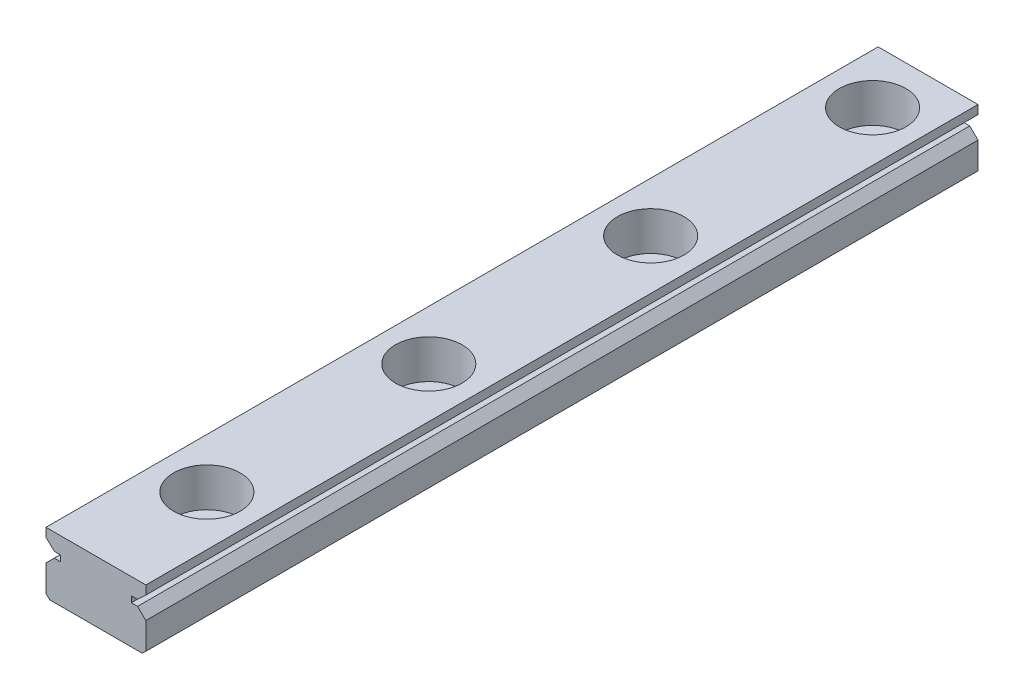
SolidWorks part; units mm, degrees
ref_plane "前视基准面" through (0, 0, 0) normal (0, 0, 1) x (1, 0, 0)
ref_plane "上视基准面" through (0, 0, 0) normal (0, 1, 0) x (1, 0, 0)
ref_plane "右视基准面" through (0, 0, 0) normal (1, 0, 0) x (0, 0, -1)
sketch "Model" plane through (0, 0, 0) normal (0, 0, 1) x (1, 0, 0)
  line L0 (172.467, 54.8604) -> (176.6229, 54.8604)
  line L1 (172.123, 60.3558) -> (176.6229, 60.3558)
  line L2 (172.123, 57.5787) -> (172.867, 58.3137)
  line L3 (172.867, 58.3137) -> (173.431, 58.3137)
  line L4 (173.431, 58.3137) -> (173.431, 58.8505)
  line L5 (173.431, 58.8505) -> (172.879, 58.8505)
  line L6 (172.879, 58.8505) -> (172.123, 59.563)
  line L7 (172.123, 55.1745) -> (172.123, 57.5787)
  line L8 (172.123, 59.563) -> (172.123, 60.3558)
  line L9 (172.123, 55.1745) -> (172.467, 54.8604)
  line L10 (180.7788, 54.8604) -> (176.6229, 54.8604)
  line L11 (181.1228, 60.3558) -> (176.6229, 60.3558)
  line L12 (181.1228, 57.5787) -> (180.3788, 58.3137)
  line L13 (180.3788, 58.3137) -> (179.8148, 58.3137)
  line L14 (179.8148, 58.3137) -> (179.8148, 58.8505)
  line L15 (179.8148, 58.8505) -> (180.3668, 58.8505)
  line L16 (180.3668, 58.8505) -> (181.1228, 59.563)
  line L17 (181.1228, 55.1745) -> (181.1228, 57.5787)
  line L18 (181.1228, 59.563) -> (181.1228, 60.3558)
  line L19 (181.1228, 55.1745) -> (180.7788, 54.8604)
  line L20 (166.623, 64.8604) -> (176.6229, 64.8604)
  line L21 (166.623, 56.8604) -> (166.623, 64.8604)
  line L22 (176.6229, 52.1745) -> (176.6229, 65.56) construction
  line L23 (166.623, 56.8604) -> (172.123, 56.8604)
  line L24 (181.1228, 60.3558) -> (176.6229, 60.3558)
  line L25 (181.1228, 57.5787) -> (180.3788, 58.3137)
  line L26 (180.3788, 58.3137) -> (179.8148, 58.3137)
  line L27 (179.8148, 58.3137) -> (179.8148, 58.8505)
  line L28 (179.8148, 58.8505) -> (180.3668, 58.8505)
  line L29 (180.3668, 58.8505) -> (181.1228, 59.563)
  line L30 (181.1228, 59.563) -> (181.1228, 60.3558)
  line L31 (186.6228, 64.8604) -> (176.6229, 64.8604)
  line L32 (186.6228, 56.8604) -> (186.6228, 64.8604)
  line L33 (186.6228, 56.8604) -> (181.1228, 56.8604)
extrude "凸台-拉伸1" add sketch "Model" along normal blind 75 contours L22 L10 L19 L17 L12 L13 L14 L15 L16 L18 L11 | L0 L22 L1 L8 L6 L5 L4 L3 L2 L7 L9
sketch "草图1" plane through (0, 60.3558, 0) normal (0, 1, 0) x (1, 0, 0)
  line L0 (176.6229, 0) -> (176.6229, -75) construction
  line L1 (181.1228, 0) -> (172.123, 0) construction
  line L2 (181.1228, -75) -> (172.123, -75) construction
  point P6 (176.6229, -5)
  point P7 (176.6229, -25)
  point P8 (176.6229, -45)
  point P9 (176.6229, -65)
  dimension "D1" = 5
  dimension "D2" = 20
  dimension "D3" = 20
  dimension "D4" = 20
hole_wizard "M6 六角头螺栓的柱形沉头孔1" positions "3D草图1" profile "草图2" counterbore size "M6" standard "GB" end condition up to next
sketch3d "3D草图1"
  point P0 (176.6229, 60.3558, 5)
  point P3 (176.6229, 60.3558, 25)
  point P6 (176.6229, 60.3558, 45)
  point P9 (176.6229, 60.3558, 65)
sketch "草图2" plane through (176.6229, 60.3558, 5) normal (1, 0, 0) x (0, 0, 1)
  line L0 (0, 0) -> (0, 5.4954)
  line L1 (0, 5.4954) -> (1.75, 5.4954)
  line L3 (1.75, 5.4954) -> (1.75, 3.5)
  line L4 (1.75, 3.5) -> (3, 3.5)
  line L5 (3, 3.5) -> (3, 0)
  line L7 (3, 0) -> (0, 0)
  line L11 (0, -6.35) -> (0, 107.95) construction
  dimension "通孔孔直径" = 3.5
  dimension "通孔孔深度" = 5.4954
  dimension "柱形沉头孔直径" = 6
  dimension "柱形沉头孔深度" = 3.5
